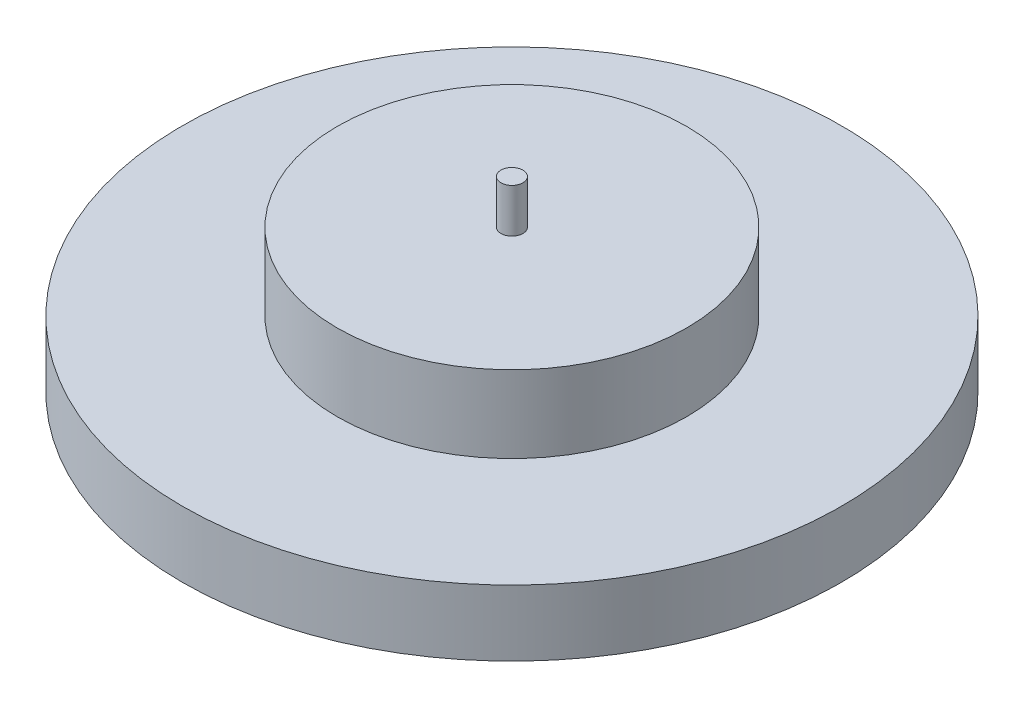
SolidWorks part; units mm, degrees
ref_plane "前视基准面" through (0, 0, 0) normal (0, 0, 1) x (1, 0, 0)
ref_plane "上视基准面" through (0, 0, 0) normal (0, 1, 0) x (1, 0, 0)
ref_plane "右视基准面" through (0, 0, 0) normal (1, 0, 0) x (0, 0, -1)
other "Configuration Table"
sketch "草图1" plane through (0, 0, 0) normal (0, 1, 0) x (1, 0, 0)
  circle A0 centre (0, 0) radius 15
  dimension "D1" = 30
extrude "凸台-拉伸1" add sketch "草图1" along normal blind 3
sketch "草图2" plane through (0, 3, 0) normal (0, 1, 0) x (1, 0, 0)
  circle A0 centre (0, 0) radius 7.95
  dimension "D1" = 15.9
extrude "凸台-拉伸2" add sketch "草图2" along normal blind 3.5
sketch "草图3" plane through (0, 6.5, 0) normal (0, 1, 0) x (1, 0, 0)
  circle A0 centre (0, 0) radius 0.5
  dimension "D1" = 1
extrude "凸台-拉伸3" add sketch "草图3" along normal blind 2
